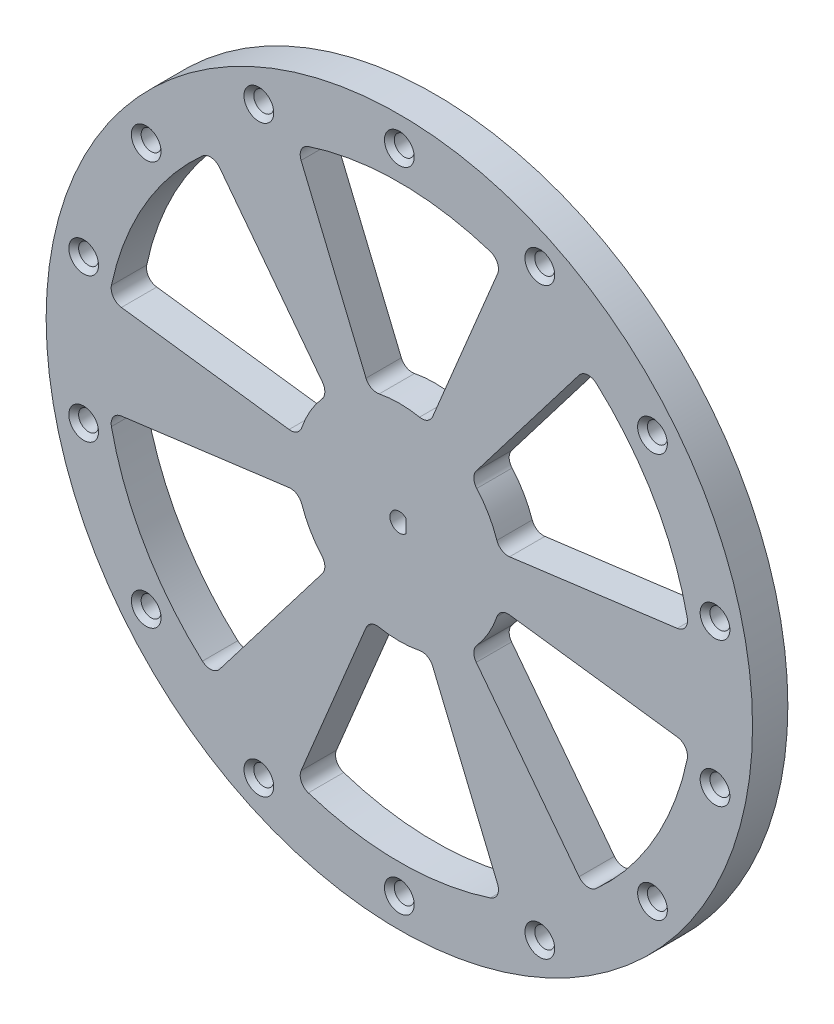
SolidWorks part; units mm, degrees
material "ABS"
ref_plane "Front Plane" through (0, 0, 0) normal (0, 0, 1) x (1, 0, 0)
ref_plane "Top Plane" through (0, 0, 0) normal (0, 1, 0) x (1, 0, 0)
ref_plane "Right Plane" through (0, 0, 0) normal (1, 0, 0) x (0, 0, -1)
sketch "Sketch1" plane through (0, 0, 0) normal (0, 0, 1) x (1, 0, 0)
  line L0 (-5, 16.7705) -> (-17.5, 46.8375)
  line L1 (5, 16.7705) -> (17.5, 46.8375)
  line L2 (0, 5.3196) -> (0, -5.2865) construction
  line L3 (17.0237, 4.0551) -> (49.3125, 8.2633)
  line L4 (12.0237, 12.7154) -> (31.8125, 38.5742)
  line L5 (12.0237, -12.7154) -> (31.8125, -38.5742)
  line L6 (17.0237, -4.0551) -> (49.3125, -8.2633)
  line L7 (-5, -16.7705) -> (-17.5, -46.8375)
  line L8 (5, -16.7705) -> (17.5, -46.8375)
  line L9 (-17.0237, -4.0551) -> (-49.3125, -8.2633)
  line L10 (-12.0237, -12.7154) -> (-31.8125, -38.5742)
  line L11 (-12.0237, 12.7154) -> (-31.8125, 38.5742)
  line L12 (-17.0237, 4.0551) -> (-49.3125, 8.2633)
  circle A0 centre (0, 0) radius 17.5
  circle A1 centre (0, 0) radius 60
  circle A2 centre (0, 0) radius 50 construction
  arc A3 (-17.5, 46.8375) -> (17.5, 46.8375) centre (0, 0) cw
  arc A4 (31.8125, 38.5742) -> (49.3125, 8.2633) centre (0, 0) cw
  arc A5 (49.3125, -8.2633) -> (31.8125, -38.5742) centre (0, 0) cw
  arc A6 (17.5, -46.8375) -> (-17.5, -46.8375) centre (0, 0) cw
  arc A7 (-31.8125, -38.5742) -> (-49.3125, -8.2633) centre (0, 0) cw
  arc A8 (-49.3125, 8.2633) -> (-31.8125, 38.5742) centre (0, 0) cw
  point P34 (0, 0)
  dimension "D1" = 120
  dimension "D2" = 35
  dimension "D3" = 100
  dimension "D4" = 35
  dimension "D5" = 10
  dimension "D6" = 6
extrude "Boss-Extrude2" add sketch "Sketch1" along normal mid plane 6 contours A0 | A1 L12 A8 L11 A0 L0 A3 L1 L4 A4 L3 L6 A5 L5 L8 A6 L7 L10 A7 L9
fillet "Fillet1" radius 2 24 edges at (5, 16.7705, 0) (-5, 16.7705, 0) (17.5, 46.8375, 0) (-17.5, 46.8375, 0) (-31.8125, -38.5742, 0) (-17.0237, 4.0551, 0) (17.0237, 4.0551, 0) (31.8125, -38.5742, 0) (49.3125, -8.2633, 0) (5, -16.7705, 0) (-17.0237, -4.0551, 0) (-5, -16.7705, 0) (17.0237, -4.0551, 0) (-31.8125, 38.5742, 0) (31.8125, 38.5742, 0) (-12.0237, 12.7154, 0) (-12.0237, -12.7154, 0) (17.5, -46.8375, 0) (49.3125, 8.2633, 0) (-17.5, -46.8375, 0) (-49.3125, 8.2633, 0) (-49.3125, -8.2633, 0) (12.0237, -12.7154, 0) (12.0237, 12.7154, 0)
sketch "Sketch4" plane through (0, 0, -3) normal (0, 0, -1) x (-1, 0, 0)
  line L1 (-1.1, 1.1619) -> (-1.1, -1.1619)
  arc A1 (-1.1, -1.1619) -> (-1.1, 1.1619) centre (0, 0) ccw
extrude "Cut-Extrude1" cut sketch "Sketch4" against normal through all both
hole_wizard "Ø5.0mm Dowel Hole1" positions "Sketch5" profile "Sketch6" hole size "Ø5.0" standard "ANSI Metric"
sketch "Sketch5" plane through (0, 0, 3) normal (0, 0, 1) x (1, 0, 0)
  point P0 (0, 55)
  dimension "D1" = 55
sketch "Sketch6" plane through (0, 55, 3) normal (1, 0, 0) x (0, -1, 0)
  line L0 (0, 0) -> (0, 21.0166)
  line L1 (0, 21.0166) -> (1.692, 20)
  line L2 (1.692, 20) -> (1.692, 0.833)
  line L3 (1.692, 0.833) -> (2.525, 0)
  line L5 (2.525, 0) -> (0, 0)
  line L6 (-1.692, 0.833) -> (-2.525, 0) construction
  line L10 (0, 21.0166) -> (-1.692, 20) construction
  line L11 (0, -6.35) -> (0, 107.95) construction
  dimension "Hole Dia." = 3.3839
  dimension "Hole Depth" = 20
  dimension "Near C'Sink Dia." = 5.05
  dimension "Near C'Sink Angle" = 90
  dimension "Drill Angle" = 118
pattern_circular "CirPattern4" count 14 over 360 about axis through (0, 0, 0) along (0, 0, 1) of "Ø5.0mm Dowel Hole1"
